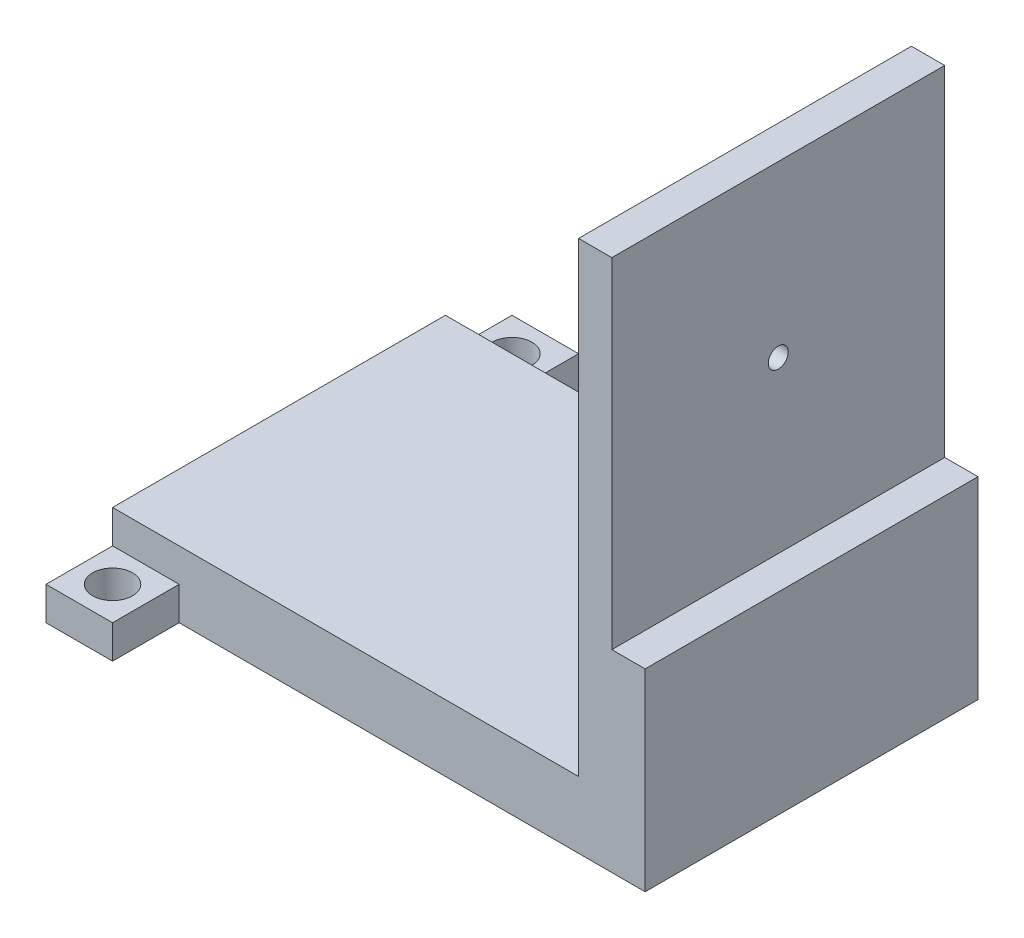
SolidWorks part; units mm, degrees
ref_plane "Front Plane" through (0, 0, 0) normal (0, 0, 1) x (1, 0, 0)
ref_plane "Top Plane" through (0, 0, 0) normal (0, 1, 0) x (1, 0, 0)
ref_plane "Right Plane" through (0, 0, 0) normal (1, 0, 0) x (0, 0, -1)
sketch "Sketch1" plane through (0, 0, 0) normal (0, 1, 0) x (1, 0, 0)
  line L1 (-26.24, 14.848) -> (53.76, 14.848)
  line L2 (-26.24, 14.848) -> (-26.24, -35.152)
  line L3 (-26.24, -35.152) -> (53.76, -35.152)
  line L4 (53.76, 14.848) -> (53.76, -35.152)
  dimension "D1" = 80
  dimension "D2" = 50
extrude "Boss-Extrude1" add sketch "Sketch1" along normal blind 10
sketch3d "3DSketch1"
  point P0 (43.3815, 5.8156, 35.152)
sketch "Sketch2" plane through (0, 0, 35.152) normal (0, 0, 1) x (1, 0, 0)
  line L0 (-26.24, 0) -> (53.76, 0) construction
  line L1 (-26.24, 10) -> (-16.24, 10)
  line L2 (-26.24, 10) -> (-26.24, 0)
  line L3 (-26.24, 0) -> (-16.24, 0)
  line L4 (-16.24, 10) -> (-16.24, 0)
extrude "Boss-Extrude2" add sketch "Sketch2" along normal blind 10
sketch "Sketch3" plane through (0, 10, 0) normal (0, 1, 0) x (1, 0, 0)
  line L1 (-16.24, -35.152) -> (-26.24, -35.152)
  line L2 (-16.24, -35.152) -> (-16.24, -45.152)
  line L3 (-16.24, -45.152) -> (-26.24, -45.152)
  line L4 (-26.24, -35.152) -> (-26.24, -45.152)
extrude "Cut-Extrude1" cut sketch "Sketch3" against normal blind 5
sketch "Sketch4" plane through (0, 5, 0) normal (0, 1, 0) x (1, 0, 0)
  circle A0 centre (-21.24, -40.152) radius 3
extrude "Cut-Extrude2" cut sketch "Sketch4" against normal blind 5
sketch "Sketch5" plane through (0, 0, -14.848) normal (0, 0, -1) x (-1, 0, 0)
  line L0 (-53.76, 0) -> (26.24, 0) construction
  line L1 (26.24, 10) -> (16.24, 10)
  line L2 (26.24, 10) -> (26.24, 0)
  line L3 (26.24, 0) -> (16.24, 0)
  line L4 (16.24, 10) -> (16.24, 0)
extrude "Boss-Extrude3" add sketch "Sketch5" along normal blind 10
sketch "Sketch6" plane through (0, 10, 0) normal (0, 1, 0) x (1, 0, 0)
  line L1 (-16.24, 14.848) -> (-26.24, 14.848)
  line L2 (-16.24, 14.848) -> (-16.24, 24.848)
  line L3 (-16.24, 24.848) -> (-26.24, 24.848)
  line L4 (-26.24, 14.848) -> (-26.24, 24.848)
extrude "Cut-Extrude3" cut sketch "Sketch6" against normal blind 5
sketch "Sketch7" plane through (0, 5, 0) normal (0, 1, 0) x (1, 0, 0)
  circle A0 centre (-21.24, 19.848) radius 3
extrude "Cut-Extrude4" cut sketch "Sketch7" against normal blind 5
sketch "Sketch10" plane through (0, 10, 0) normal (0, 1, 0) x (1, 0, 0)
  line L0 (-26.24, -35.152) -> (53.76, -35.152) construction
  line L1 (53.76, 14.848) -> (43.76, 14.848)
  line L2 (53.76, 14.848) -> (53.76, -35.152)
  line L3 (53.76, -35.152) -> (43.76, -35.152)
  line L4 (43.76, 14.848) -> (43.76, -35.152)
extrude "Boss-Extrude4" add sketch "Sketch10" along normal blind 70
sketch "Sketch11" plane through (53.76, 0, 0) normal (1, 0, 0) x (0, 0, -1)
  line L0 (-35.152, 80) -> (-35.152, 0) construction
  line L1 (14.848, 80) -> (-35.152, 80)
  line L2 (14.848, 80) -> (14.848, 29)
  line L3 (14.848, 29) -> (-35.152, 29)
  line L4 (-35.152, 80) -> (-35.152, 29)
extrude "Cut-Extrude5" cut sketch "Sketch11" against normal blind 5
sketch "Sketch12" plane through (48.76, 0, 0) normal (1, 0, 0) x (0, 0, -1)
  circle A0 centre (-10.152, 54.5) radius 1.5
extrude "Cut-Extrude7" cut sketch "Sketch12" against normal blind 10
